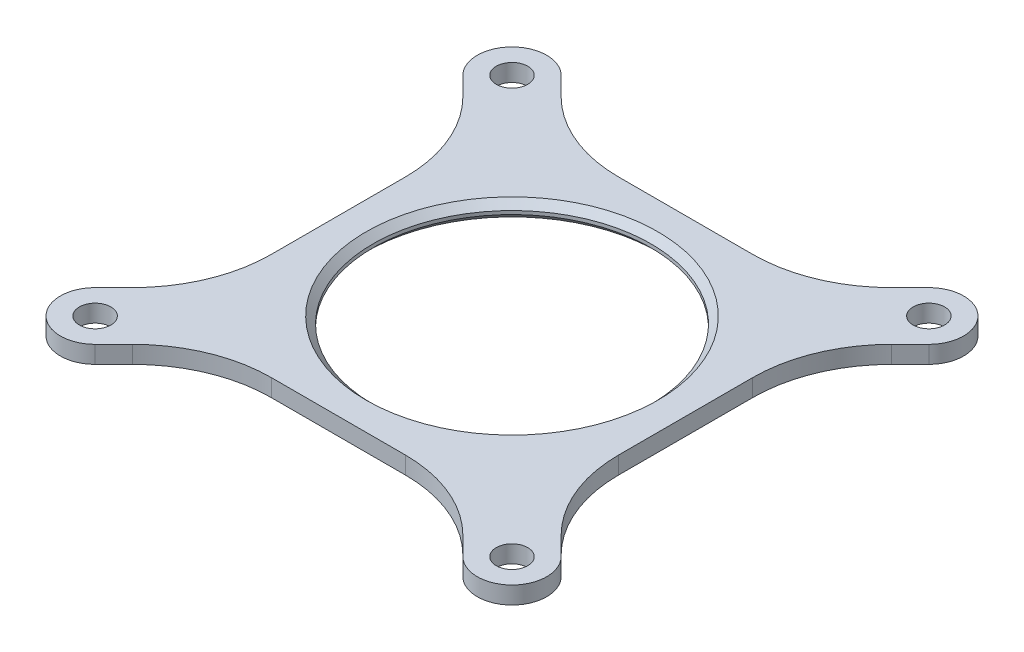
SolidWorks part; units mm, degrees
ref_plane "Front Plane" through (0, 0, 0) normal (0, 0, 1) x (1, 0, 0)
ref_plane "Top Plane" through (0, 0, 0) normal (0, 1, 0) x (1, 0, 0)
ref_plane "Right Plane" through (0, 0, 0) normal (1, 0, 0) x (0, 0, -1)
sketch "Sketch1" plane through (0, 0, 0) normal (0, 1, 0) x (1, 0, 0)
  line L0 (0, 113.0266) -> (0, -125.0112) construction
  line L1 (-45.5395, 63.5) -> (45.5395, 63.5)
  line L2 (-63.5, 45.5395) -> (-63.5, -45.5395)
  line L3 (-45.5395, -63.5) -> (45.5395, -63.5)
  line L4 (63.5, 45.5395) -> (63.5, -45.5395)
  line L5 (-117.7791, 0) -> (166.9571, 0) construction
  line L6 (-115.9329, -115.9329) -> (127.4148, 127.4148) construction
  line L7 (-155.6684, 155.6684) -> (117.2681, -117.2681) construction
  line L8 (-67.2197, 85.1803) -> (-45.5395, 63.5)
  line L9 (-85.1803, 67.2197) -> (-63.5, 45.5395)
  line L10 (85.1803, 67.2197) -> (63.5, 45.5395)
  line L11 (67.2197, 85.1803) -> (45.5395, 63.5)
  line L12 (85.1803, -67.2197) -> (63.5, -45.5395)
  line L13 (67.2197, -85.1803) -> (45.5395, -63.5)
  line L14 (-67.2197, -85.1803) -> (-45.5395, -63.5)
  line L15 (-85.1803, -67.2197) -> (-63.5, -45.5395)
  circle A0 centre (0, 0) radius 50.8
  arc A1 (-67.2197, 85.1803) -> (-85.1803, 67.2197) centre (-76.2, 76.2) ccw
  arc A2 (85.1803, 67.2197) -> (67.2197, 85.1803) centre (76.2, 76.2) ccw
  arc A3 (67.2197, -85.1803) -> (85.1803, -67.2197) centre (76.2, -76.2) ccw
  arc A4 (-85.1803, -67.2197) -> (-67.2197, -85.1803) centre (-76.2, -76.2) ccw
  point P39 (-83.6801, -65.9366)
  point P40 (0, 0)
  point P41 (0, 0)
  point P42 (0, 0)
  dimension "D1" = 101.6
  dimension "D6" = 25.4
  dimension "D4" = 63.5
  dimension "D5" = 63.5
  dimension "D7" = 152.4
  dimension "D8" = 76.2
  dimension "D9" = 76.2
  dimension "D10" = 45
  dimension "D11" = 45
  dimension "D12" = 152.4
  dimension "D2" = 127
  dimension "D3" = 127
extrude "Boss-Extrude1" add sketch "Sketch1" along normal blind 6.35 contours L3 L13 A3 L12 L4 L10 A2 L11 L1 L8 A1 L9 L2 L15 A4 L14
sketch "Sketch2" plane through (0, 6.35, 0) normal (0, 1, 0) x (1, 0, 0)
  circle A0 centre (0, 0) radius 50.8
  dimension "D1" = 101.6
extrude "Cut-Extrude1" cut sketch "Sketch2" against normal blind 6.35
fillet "Fillet1" radius 50.8 8 edges at (63.5, 3.175, -45.5395) (63.5, 3.175, 45.5395) (45.5395, 3.175, -63.5) (-63.5, 3.175, 45.5395) (-63.5, 3.175, -45.5395) (45.5395, 3.175, 63.5) (-45.5395, 3.175, 63.5) (-45.5395, 3.175, -63.5)
sketch "Sketch3" plane through (0, 6.35, 0) normal (0, 1, 0) x (1, 0, 0)
  line L0 (0, 106.4082) -> (0, -109.7396) construction
  line L1 (-119.8667, 0) -> (135.7515, 0) construction
  line L2 (-102.9412, 102.9412) -> (118.4978, -118.4978) construction
  line L3 (-99.1359, -99.1359) -> (104.8295, 104.8295) construction
  point P9 (-76.2, 76.2)
  point P10 (76.2, 76.2)
  point P11 (76.2, -76.2)
  point P12 (-76.2, -76.2)
  point P13 (0, 0)
  point P14 (0, 0)
  point P15 (0, 0)
  point P16 (0, 0)
  dimension "D1" = 45
  dimension "D2" = 45
  dimension "D3" = 152.4
  dimension "D4" = 152.4
hole_wizard "1/2-20 Tapped Hole1" positions "3DSketch1" profile "Sketch5" tap size "1/2-20" standard "ANSI Inch"
sketch3d "3DSketch1"
  point P0 (-76.2, 6.35, -76.2)
  point P3 (76.2, 6.35, -76.2)
  point P5 (76.2, 6.35, 76.2)
  point P8 (-76.2, 6.35, 76.2)
  point P12 (76.2, 6.35, -76.2)
sketch "Sketch5" plane through (-76.2, 6.35, -76.2) normal (1, 0, 0) x (0, 0, 1)
  line L0 (0, 0) -> (0, 32.6676)
  line L1 (0, 32.6676) -> (5.7544, 29.21)
  line L2 (5.7544, 29.21) -> (5.7544, 0)
  line L5 (5.7544, 0) -> (0, 0)
  line L10 (0, 32.6676) -> (-5.7544, 29.21) construction
  line L11 (0, -6.35) -> (0, 107.95) construction
  dimension "Tap Drill Dia." = 11.5087
  dimension "Tap Drill Depth" = 29.21
  dimension "Drill Angle" = 118
cosmetic thread "Hole Thread1" parameters "D1"=6.35, "D2"=12.7
cosmetic thread "Hole Thread2" parameters "D1"=6.35, "D2"=12.7
cosmetic thread "Hole Thread3" parameters "D1"=6.35, "D2"=12.7
cosmetic thread "Hole Thread4" parameters "D1"=6.35, "D2"=12.7
chamfer "Chamfer1" distance 2.54 angle 45 2 edges at (0, 0, 50.8) (0, 6.35, 50.8)
equation "\"D4@Sketch1\"=\"D2@Sketch1\"/2"
equation "\"D5@Sketch1\"= \"D4@Sketch1\""
equation "\"D8@Sketch1\"=\"D7@Sketch1\"/2"
equation "\"D9@Sketch1\"=\"D8@Sketch1\""
equation "\"D12@Sketch1\"=\"D7@Sketch1\""
